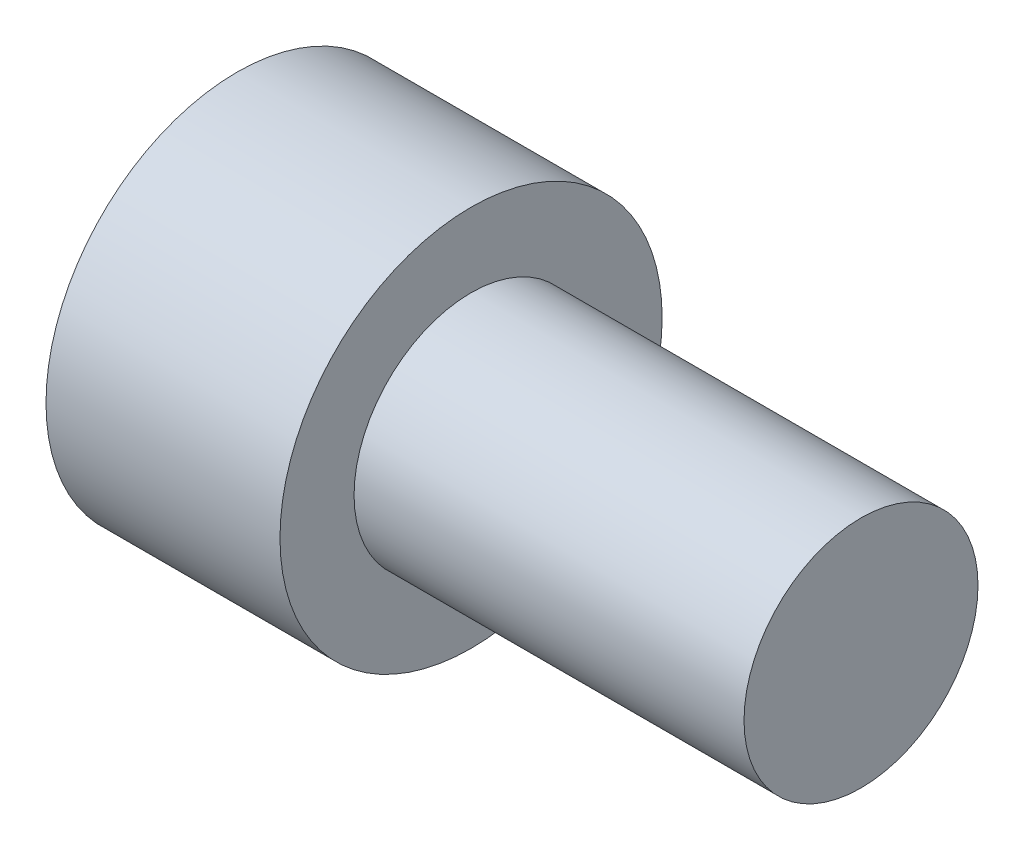
SolidWorks part; units mm, degrees
ref_plane "Front Plane" through (0, 0, 0) normal (0, 0, 1) x (1, 0, 0)
ref_plane "Top Plane" through (0, 0, 0) normal (0, 1, 0) x (1, 0, 0)
ref_plane "Right Plane" through (0, 0, 0) normal (1, 0, 0) x (0, 0, -1)
sketch "Sketch1" plane through (0, 0, 0) normal (0, 1, 0) x (1, 0, 0)
  line L0 (19.05, 15.5575) -> (19.05, 0)
  line L1 (0, 0) -> (19.05, 0) construction
  line L2 (0, 0) -> (0, 19.05) construction
  line L3 (19.05, 0) -> (0, 0)
  line L5 (9.525, 0) -> (9.525, 32.3839) construction
  line L6 (8.73, 15.5575) -> (19.05, 15.5575)
  line L8 (0, 0) -> (0, 15.5575)
  line L9 (0, 6.329) -> (0, 8.02)
  line L10 (0, 9.525) -> (0, 10.2981)
  line L13 (0, 8.02) -> (0, 19.05)
  line L16 (0.79, 15.5575) -> (8.73, 15.5575)
  line L17 (0, 19.05) -> (0, 15.5575)
  line L18 (0, 15.5575) -> (0.79, 15.5575)
  dimension "D1" = 15.5575
  dimension "D2" = 19.05
  dimension "D3" = 19.05
revolve "Revolve1" add sketch "Sketch1" angle 360 about L1
sketch3d "3DSketch1" plane through (0, 0, 0) normal (0, 0, 1) x (1, 0, 0)
  dimension "D1" = 10
sketch "Sketch4" plane through (19.05, 0, 0) normal (1, 0, 0) x (0, 0, -1)
  circle A0 centre (0, 0) radius 9.525
extrude "Boss-Extrude1" add sketch "Sketch4" along normal blind 31.75
